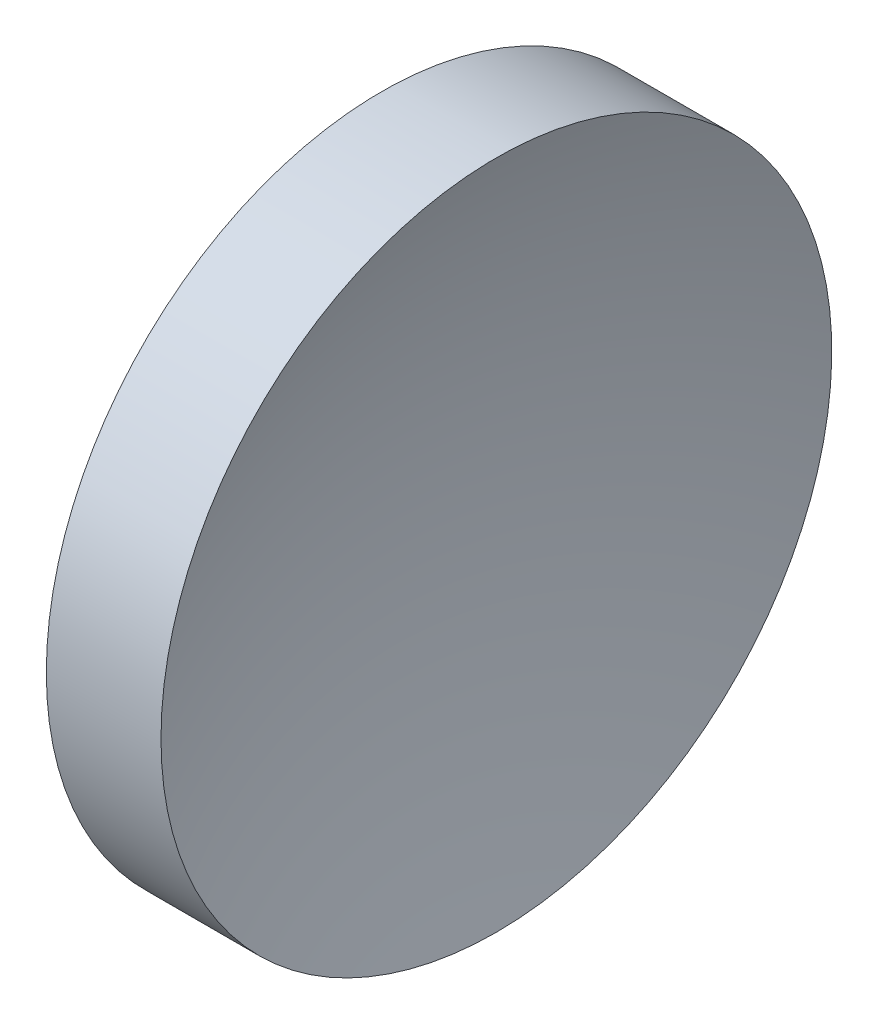
SolidWorks part; units mm, degrees
ref_plane "前视基准面" through (0, 0, 0) normal (0, 0, 1) x (1, 0, 0)
ref_plane "上视基准面" through (0, 0, 0) normal (0, 1, 0) x (1, 0, 0)
ref_plane "右视基准面" through (0, 0, 0) normal (1, 0, 0) x (0, 0, -1)
sketch "草图1" plane through (0, 0, 0) normal (0, 0, 1) x (1, 0, 0)
  line L0 (111.9552, 71.194) -> (137.836, 71.194) construction
  line L1 (119.5068, 71.194) -> (119.5068, 83.894)
  line L2 (119.5068, 83.894) -> (123.8492, 83.894)
  line L3 (121.5068, 71.194) -> (119.5068, 71.194)
  arc A0 (123.8492, 83.894) -> (121.5068, 71.194) centre (157.1068, 71.194) ccw
revolve "旋转1" add sketch "草图1" angle 360 about L0
